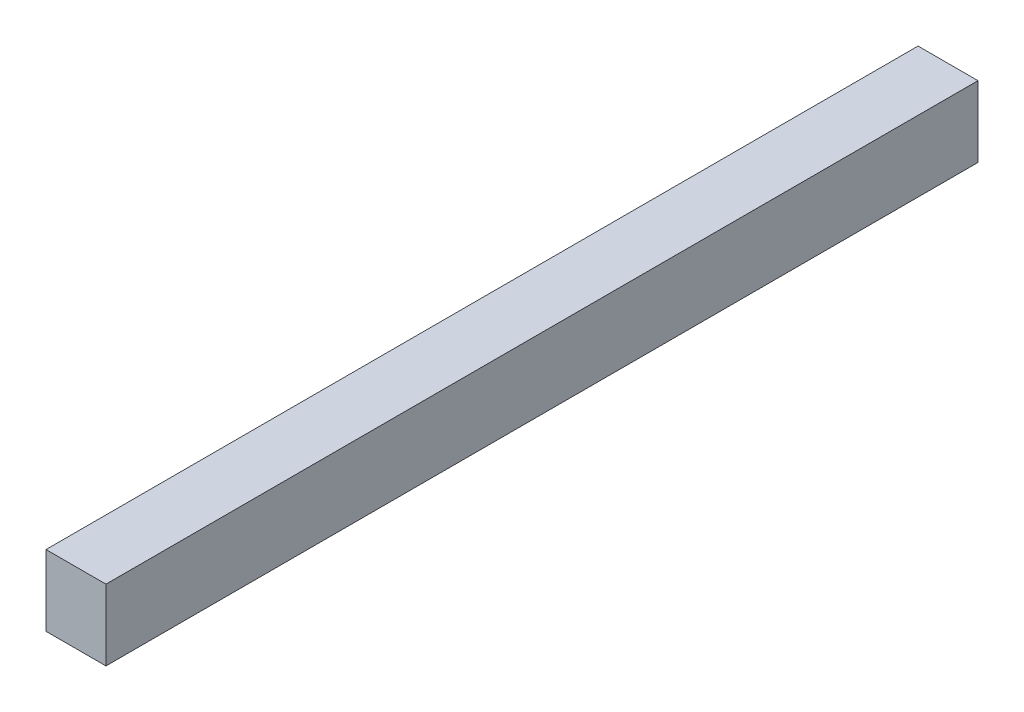
SolidWorks part; units mm, degrees
ref_plane "Front Plane" through (0, 0, 0) normal (0, 0, 1) x (1, 0, 0)
ref_plane "Top Plane" through (0, 0, 0) normal (0, 1, 0) x (1, 0, 0)
ref_plane "Right Plane" through (0, 0, 0) normal (1, 0, 0) x (0, 0, -1)
sketch "Sketch1" plane through (0, 0, 0) normal (0, 0, 1) x (1, 0, 0)
  line L1 (-1.375, 1.625) -> (1.375, 1.625)
  line L2 (-1.375, 1.625) -> (-1.375, -1.625)
  line L3 (-1.375, -1.625) -> (1.375, -1.625)
  line L4 (1.375, 1.625) -> (1.375, -1.625)
  line L5 (-1.375, 1.625) -> (1.375, -1.625) construction
  line L6 (-1.375, -1.625) -> (1.375, 1.625) construction
  point P0 (0, 0)
  dimension "D1" = 2.75
  dimension "D2" = 3.25
extrude "Boss-Extrude1" add sketch "Sketch1" along normal blind 40
